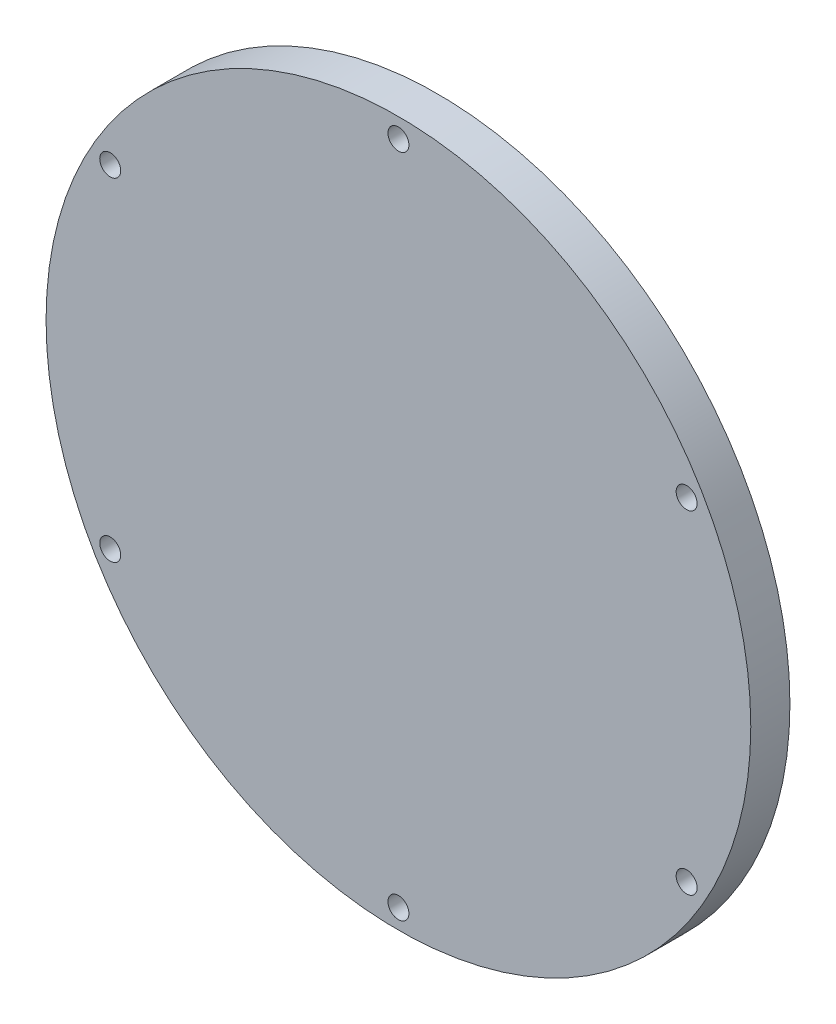
SolidWorks part; units mm, degrees
ref_plane "Front Plane" through (0, 0, 0) normal (0, 0, 1) x (1, 0, 0)
ref_plane "Top Plane" through (0, 0, 0) normal (0, 1, 0) x (1, 0, 0)
ref_plane "Right Plane" through (0, 0, 0) normal (1, 0, 0) x (0, 0, -1)
sketch "Sketch2" plane through (0, 0, 0) normal (0, 0, 1) x (1, 0, 0)
  circle A0 centre (0, 0) radius 57.15
  dimension "D1" = 114.3
extrude "Boss-Extrude1" add sketch "Sketch2" along normal blind 6.35
sketch "Sketch6" plane through (0, 0, 6.35) normal (0, 0, 1) x (1, 0, 0)
  line L0 (0, -53.975) -> (0, 53.975) construction
  line L1 (0, 0) -> (57.15, 0) construction
  circle A0 centre (0, 53.975) radius 1.7
  circle A1 centre (0, 0) radius 57.15 construction
  dimension "D2" = 3.4
  dimension "D1" = 107.95
extrude "Cut-Extrude4" cut sketch "Sketch6" against normal through all
pattern_circular "CirPattern3" count 6 over 360 about axis through (0, 0, 0) along (0, 0, 1) of "Cut-Extrude4"
